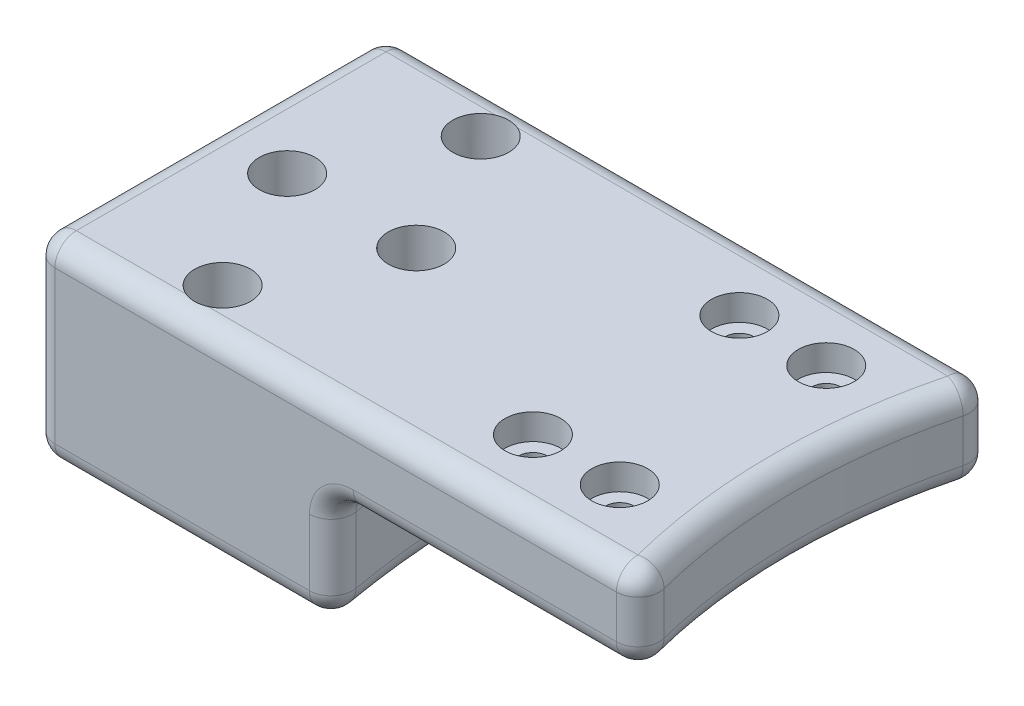
SolidWorks part; units mm, degrees
ref_plane "Front Plane" through (0, 0, 0) normal (0, 0, 1) x (1, 0, 0)
ref_plane "Top Plane" through (0, 0, 0) normal (0, 1, 0) x (1, 0, 0)
ref_plane "Right Plane" through (0, 0, 0) normal (1, 0, 0) x (0, 0, -1)
sketch "Sketch1" plane through (0, 0, 0) normal (0, 0, 1) x (1, 0, 0)
  line L0 (0, 0) -> (-46583.1629, 0) construction
  line L1 (0, -931.6633) -> (0, 45651.4997) construction
  line L2 (-70, 0) -> (-105, 0)
  line L3 (-105, 0) -> (-105, -12.7)
  line L4 (-105, -12.7) -> (-143, -12.7)
  line L5 (-143, -12.7) -> (-143, 10)
  line L6 (-143, 10) -> (-70, 10)
  line L7 (-70, 10) -> (-70, 0)
  point P4 (-70, 0)
  dimension "D1" = 70
  dimension "D2" = 12.7
  dimension "D3" = 10
  dimension "D4" = 38
  dimension "D5" = 35
extrude "Boss-Extrude1" add sketch "Sketch1" along normal mid plane 41
sketch "Sketch2" plane through (0, 10, 0) normal (0, 1, 0) x (1, 0, 0)
  line L0 (-55, 0) -> (55, 0) construction
  line L1 (-70, -20.5) -> (-70, 20.5) construction
  circle A0 centre (-5, 0) radius 70
  dimension "D1" = 140
  dimension "D2" = 65
extrude "Cut-Extrude1" cut sketch "Sketch2" against normal blind 41
sketch "Sketch3" plane through (0, 0, 0) normal (0, 1, 0) x (1, 0, 0)
  line L0 (-55, 0) -> (55, 0) construction
  line L1 (-105, -20.5) -> (-105, 20.5) construction
  circle A0 centre (-10, 0) radius 100
  dimension "D1" = 200
  dimension "D2" = 95
extrude "Cut-Extrude2" cut sketch "Sketch3" against normal blind 41
fillet "Fillet1" radius 2.5 18 edges at (-107.8762, -6.35, -20.5) (-107.8762, -6.35, 20.5) (-75, 0, 0) (-110, -12.7, 0) (-110, 0, 0) (-89.9036, 0, -20.5) (-89.9036, 0, 20.5) (-125.4381, -12.7, -20.5) (-143, -12.7, 0) (-125.4381, -12.7, 20.5) (-107.4655, 10, -20.5) (-143, 10, 0) (-107.4655, 10, 20.5) (-75, 10, 0) (-71.9309, 5, -20.5) (-71.9309, 5, 20.5) (-143, -1.35, -20.5) (-143, -1.35, 20.5)
hole_wizard "CBORE for M3 SHCS1" positions "Sketch4" profile "Sketch5" counterbore size "M3" standard "ANSI Metric"
sketch "Sketch4" plane through (0, 10, 0) normal (0, 1, 0) x (1, 0, 0)
  line L0 (-12.485, 0) -> (12.485, 0) construction
  line L1 (-126.5, 15) -> (-126.5, -15)
  line L3 (-134, 0) -> (-119, 0)
  line L4 (-143, -18) -> (-143, 18) construction
  point P0 (-134, 0)
  point P4 (-119, 0)
  point P6 (-126.5, 15)
  point P8 (-126.5, -15)
  point P21 (-126.5, 0)
  point P22 (-126.5, 0)
  dimension "D1" = 15
  dimension "D2" = 30
  dimension "D3" = 9
sketch "Sketch5" plane through (-134, 10, 0) normal (1, 0, 0) x (0, 0, 1)
  line L0 (0, 0) -> (0, 46.0215)
  line L1 (0, 46.0215) -> (1.7, 45)
  line L2 (1.7, 45) -> (1.7, 5)
  line L3 (1.7, 5) -> (3.25, 5)
  line L4 (3.25, 5) -> (3.25, 0)
  line L5 (3.25, 0) -> (0, 0)
  line L10 (0, 46.0215) -> (-1.7, 45) construction
  line L11 (0, -6.35) -> (0, 107.95) construction
  dimension "Hole Dia." = 3.4
  dimension "Hole Depth" = 45
  dimension "C'Bore Dia." = 6.5
  dimension "C'Bore Depth" = 5
  dimension "Drill Angle" = 118
sketch "Sketch6" plane through (0, 0, 0) normal (0, 1, 0) x (1, 0, 0)
  line L1 (-12.485, 0) -> (12.485, 0) construction
  circle A0 centre (0, 0) radius 70 construction
  circle A1 centre (0, 0) radius 100 construction
  circle A2 centre (0, 0) radius 84.2 construction
  circle A3 centre (0, 0) radius 94.2 construction
  point P4 (-93.4325, 12)
  point P8 (-93.4325, -12)
  point P9 (-83.3405, -12)
  point P12 (-83.3405, 12)
  dimension "D1" = 140
  dimension "D2" = 200
  dimension "D3" = 168.4
  dimension "D4" = 188.4
  dimension "D5" = 12
  dimension "D6" = 12
hole_wizard "CBORE for M3 SHCS2" positions "Sketch7" profile "Sketch8" counterbore size "M3" standard "ANSI Metric"
sketch "Sketch7" plane through (0, 10, 0) normal (0, 1, 0) x (1, 0, 0)
  point P0 (-93.4325, 12)
  point P6 (-93.4325, -12)
  point P11 (-83.3405, 12)
  point P14 (-83.3405, -12)
sketch "Sketch8" plane through (-93.4325, 10, -12) normal (1, 0, 0) x (0, 0, 1)
  line L0 (0, 0) -> (0, 46.0215)
  line L1 (0, 46.0215) -> (1.7, 45)
  line L2 (1.7, 45) -> (1.7, 3)
  line L3 (1.7, 3) -> (3.25, 3)
  line L4 (3.25, 3) -> (3.25, 0)
  line L5 (3.25, 0) -> (0, 0)
  line L10 (0, 46.0215) -> (-1.7, 45) construction
  line L11 (0, -6.35) -> (0, 107.95) construction
  dimension "Hole Dia." = 3.4
  dimension "Hole Depth" = 45
  dimension "C'Bore Dia." = 6.5
  dimension "C'Bore Depth" = 3
  dimension "Drill Angle" = 118
